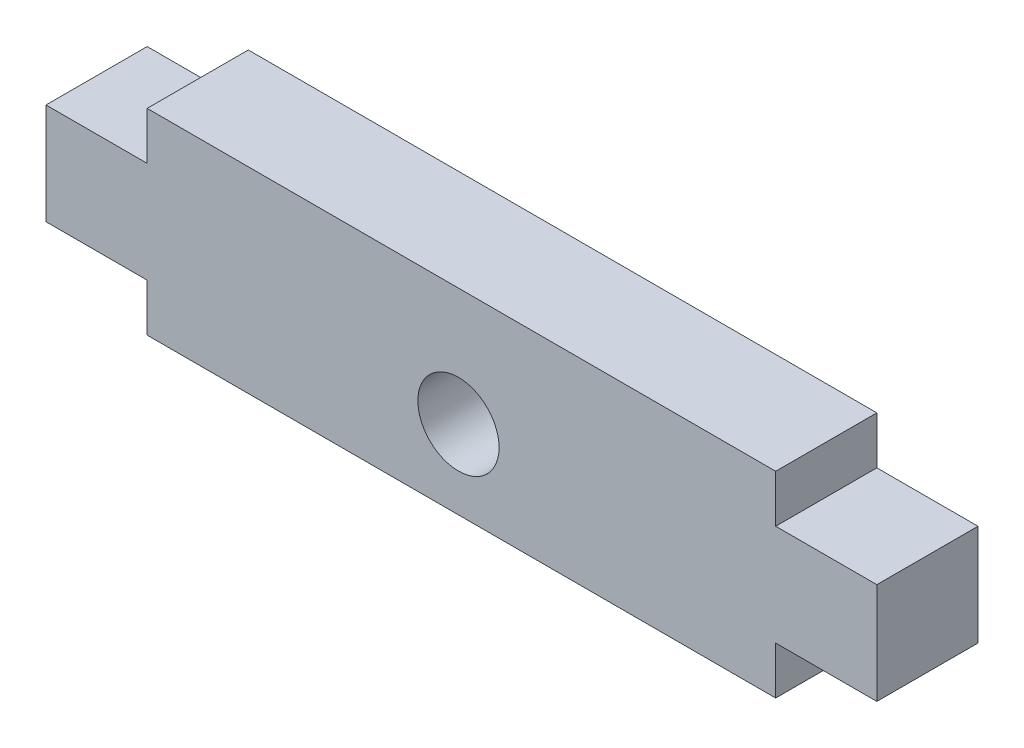
SolidWorks part; units mm, degrees
ref_plane "Front Plane" through (0, 0, 0) normal (0, 0, 1) x (1, 0, 0)
ref_plane "Top Plane" through (0, 0, 0) normal (0, 1, 0) x (1, 0, 0)
ref_plane "Right Plane" through (0, 0, 0) normal (1, 0, 0) x (0, 0, -1)
sketch "Sketch1" plane through (0, 0, 0) normal (0, 0, 1) x (1, 0, 0)
  line L0 (0, 2.425) -> (0, 7.575)
  line L1 (0, -55) -> (0, 55) construction
  line L2 (0, 7.575) -> (5.15, 7.575)
  line L3 (5.15, 10) -> (5.15, 7.575)
  line L4 (55, 0) -> (-55, 0) construction
  line L5 (5.15, 0) -> (37.15, 0)
  line L6 (37.15, 7.575) -> (37.15, 10)
  line L7 (37.15, 7.575) -> (42.3, 7.575)
  line L8 (42.3, 7.575) -> (42.3, 2.425)
  line L9 (42.3, 2.425) -> (37.15, 2.425)
  line L10 (37.15, 2.425) -> (37.15, 0)
  line L11 (37.15, 10) -> (5.15, 10)
  line L12 (5.15, 2.425) -> (5.15, 0)
  line L13 (5.15, 2.425) -> (0, 2.425)
  dimension "D1" = 32
  dimension "D2" = 5.15
  dimension "D3" = 10
  dimension "D4" = 5.15
extrude "Boss-Extrude1" add sketch "Sketch1" along normal blind 5.15
sketch "Sketch2" plane through (0, 0, 5.15) normal (0, 0, 1) x (1, 0, 0)
  line L0 (55, 0) -> (-55, 0) construction
  circle A0 centre (21, 4) radius 2.0675
  dimension "D1" = 4.135
  dimension "D2" = 4
extrude "Cut-Extrude1" cut sketch "Sketch2" against normal through all
